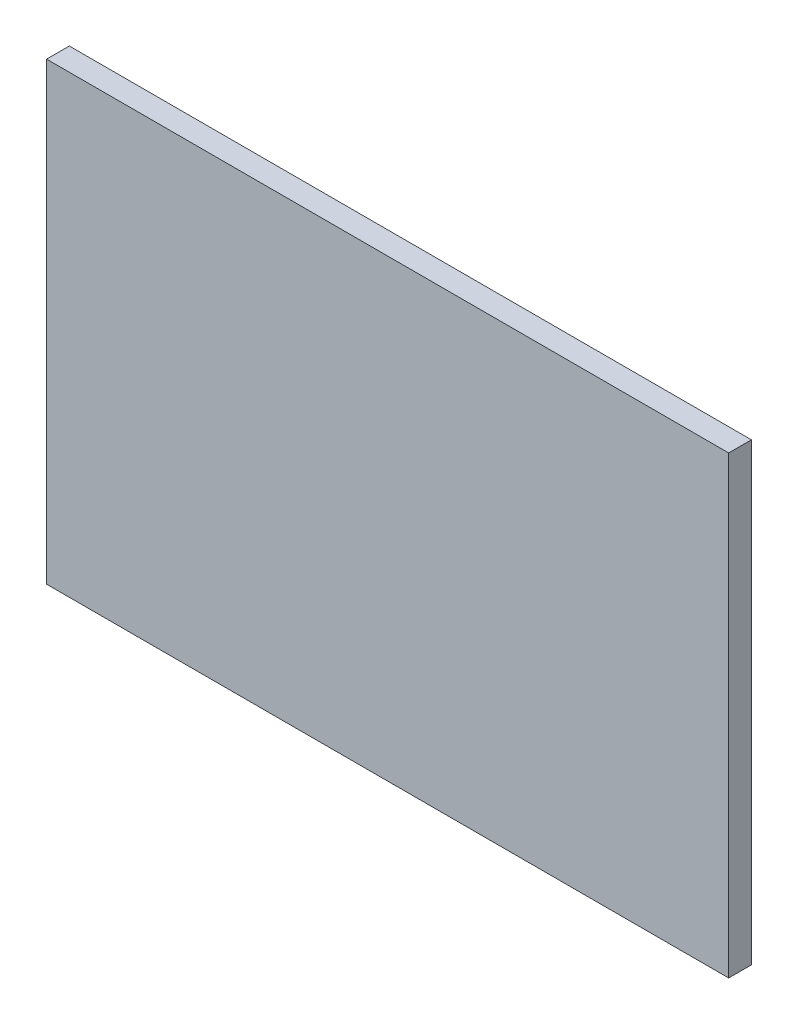
SolidWorks part; units mm, degrees
ref_plane "Plan de face" through (0, 0, 0) normal (0, 0, 1) x (1, 0, 0)
ref_plane "Plan de dessus" through (0, 0, 0) normal (0, 1, 0) x (1, 0, 0)
ref_plane "Plan de droite" through (0, 0, 0) normal (1, 0, 0) x (0, 0, -1)
sketch "Esquisse1" plane through (0, 0, 0) normal (0, 0, 1) x (1, 0, 0)
  line L1 (0, 0) -> (150, 0)
  line L2 (0, 0) -> (0, 100)
  line L3 (0, 100) -> (150, 100)
  line L4 (150, 0) -> (150, 100)
  dimension "D1" = 100
  dimension "D2" = 150
extrude "Boss.-Extru.1" add sketch "Esquisse1" along normal blind 5
